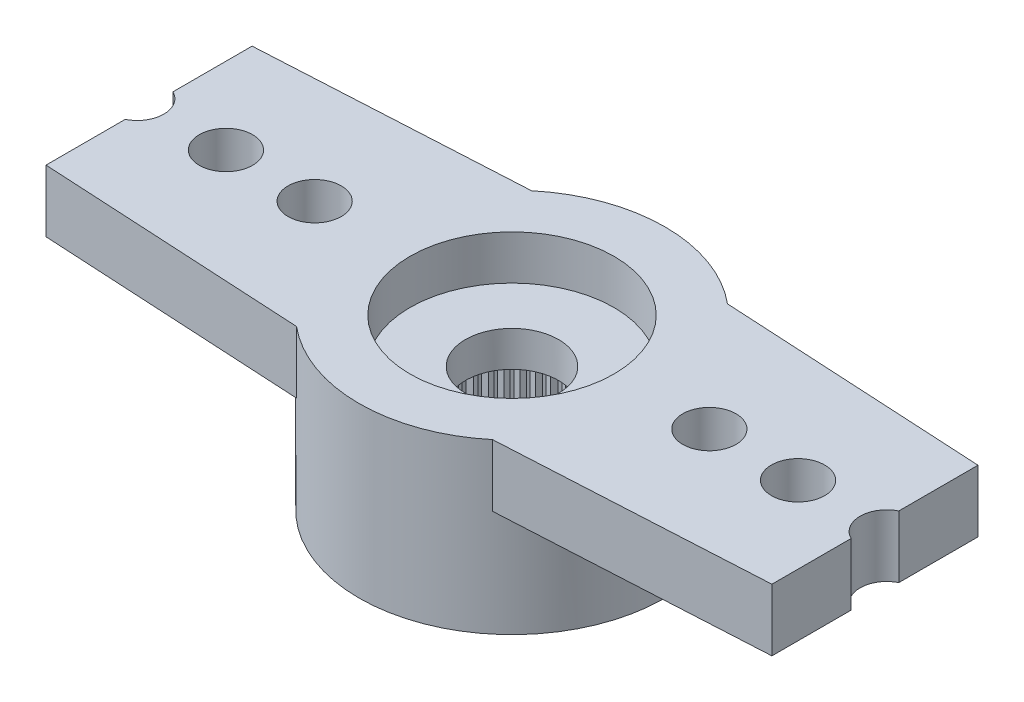
SolidWorks part; units mm, degrees
material "PVC Rígido"
ref_plane "Plano frontal" through (0, 0, 0) normal (0, 0, 1) x (1, 0, 0)
ref_plane "Plano superior" through (0, 0, 0) normal (0, 1, 0) x (1, 0, 0)
ref_plane "Plano direito" through (0, 0, 0) normal (1, 0, 0) x (0, 0, -1)
sketch "Esboço1" plane through (0, 0, 0) normal (0, 1, 0) x (1, 0, 0)
  line L0 (0, 0) -> (-14.05, 0) construction
  line L1 (-14.1591, 1.997) -> (-2.2091, 2.65)
  line L2 (-2.2091, -2.65) -> (-14.1591, -1.997)
  arc A0 (-2.2091, -2.65) -> (-2.2091, 2.65) centre (0, 0) ccw
  arc A1 (-14.1591, 1.997) -> (-14.1591, -1.997) centre (-14.05, 0) ccw
  dimension "D1" = 6.9
  dimension "D2" = 4
  dimension "D3" = 19.5
  dimension "D4" = 5.3
extrude "Ressalto-extrusão1" add sketch "Esboço1" against normal blind 1.4
sketch "Esboço2" plane through (0, -1.4, 0) normal (0, -1, 0) x (1, 0, 0)
  arc A0 (-2.2091, -2.65) -> (-2.2091, 2.65) centre (0, 0) ccw construction
  circle A1 centre (0, 0) radius 3.45
extrude "Ressalto-extrusão2" add sketch "Esboço2" along normal offset from surface (2.4 mm away) 3.8 up to face at (-7.242, 0, 0)
hole_wizard "Furo4" positions "Esboço9" profile "Esboço10" legacy end condition through all
sketch "Esboço9" plane through (0, 0, 0) normal (0, 1, 0) x (1, 0, 0)
  line L1 (-14.45, 0) -> (0, 0) construction
  arc A2 (-14.1591, 1.997) -> (-14.1591, -1.997) centre (-14.05, 0) ccw construction
  point P0 (-14.45, 0)
  point P19 (-16.05, 0)
  dimension "D1" = 1.6
sketch "Esboço10" plane through (-14.45, 0, 0) normal (1, 0, 0) x (0, 0, 1)
  line L0 (0, 0) -> (0, 3.8)
  line L1 (0, 3.8) -> (0.6, 3.8)
  line L2 (0.6, 3.8) -> (0.6, 0)
  line L3 (0.6, 0) -> (0, 0)
  line L4 (0, 110) -> (0, -10) construction
  dimension "Diameter" = 1.2
  dimension "Depth" = 3.8
pattern_linear "Padrão linear1" count 6 spacing 2 along (1, 0, 0) of "Furo4"
pattern_circular "PadrãoCircular2" count 2 over 360 about axis through (0, 0, 0) along (0, 1, 0) of "Ressalto-extrusão1", "Furo4", "Padrão linear1"
hole_wizard "Furo1" positions "Esboço3" profile "Esboço4" legacy
sketch "Esboço3" plane through (0, -3.8, 0) normal (0, -1, 0) x (-1, 0, 0)
  point P0 (0, 0)
sketch "Esboço4" plane through (0, -3.8, 0) normal (1, 0, 0) x (0, 0, -1)
  line L0 (0, 0) -> (0, 2)
  line L1 (0, 2) -> (2.475, 2)
  line L2 (2.475, 2) -> (2.475, 0)
  line L3 (2.475, 0) -> (0, 0)
  line L4 (0, 110) -> (0, -10) construction
  dimension "Diameter" = 4.95
  dimension "Depth" = 2
hole_wizard "Furo2" positions "Esboço5" profile "Esboço6" legacy
sketch "Esboço5" plane through (0, 0, 0) normal (0, 1, 0) x (1, 0, 0)
  point P0 (0, 0)
sketch "Esboço6" plane through (0, 0, 0) normal (1, 0, 0) x (0, 0, 1)
  line L0 (0, 0) -> (0, 1)
  line L1 (0, 1) -> (2.3, 1)
  line L2 (2.3, 1) -> (2.3, 0)
  line L3 (2.3, 0) -> (0, 0)
  line L4 (0, 110) -> (0, -10) construction
  dimension "Diameter" = 4.6
  dimension "Depth" = 1
hole_wizard "Furo3" positions "Esboço7" profile "Esboço8" legacy end condition through all
sketch "Esboço7" plane through (0, 0, 0) normal (0, 1, 0) x (1, 0, 0)
  point P0 (0, 0)
sketch "Esboço8" plane through (0, 0, 0) normal (1, 0, 0) x (0, 0, 1)
  line L0 (0, 0) -> (0, 3.8)
  line L1 (0, 3.8) -> (1.05, 3.8)
  line L2 (1.05, 3.8) -> (1.05, 0)
  line L3 (1.05, 0) -> (0, 0)
  line L4 (0, 110) -> (0, -10) construction
  dimension "Diameter" = 2.1
  dimension "Depth" = 3.8
sketch "Esboço11" plane through (0, -3.8, 0) normal (0, -1, 0) x (1, 0, 0)
  line L0 (-0.0981, 2.4731) -> (0, 2.375)
  line L1 (0, 2.375) -> (0.0981, 2.4731)
  line L2 (0, 0) -> (0, 2.475) construction
  circle A0 centre (0, 0) radius 2.375 construction
  circle A1 centre (0, 0) radius 2.475
  arc A2 (0.0981, 2.4731) -> (-0.0981, 2.4731) centre (0, 0) ccw
  dimension "D3" = 4.75
  dimension "D2" = 0.1
  dimension "D1" = 0
extrude "Ressalto-extrusão3" add sketch "Esboço11" against normal up to surface (2 mm away) up to face at (0, -1.8, 1.05)
pattern_circular "PadrãoCircular1" count 60 over 360 about axis through (0, 0, 0) along (0, 1, 0) of "Ressalto-extrusão3"
sketch "Szkic1" plane through (0, 0, 0) normal (0, 1, 0) x (1, 0, 0)
  line L0 (-8.1841, 2.3235) -> (-8.1841, -2.3235)
  line L1 (-2.2091, 2.65) -> (-14.1591, 1.997) construction
  line L2 (-14.1591, -1.997) -> (-2.2091, -2.65) construction
  line L3 (0, 0) -> (0, 3.45) construction
  line L4 (8.1841, 2.3235) -> (8.1841, -2.3235)
  line L5 (-8.1841, 2.3235) -> (-14.1591, 1.997)
  line L6 (-8.1841, -2.3235) -> (-14.1591, -1.997)
  line L7 (8.1841, -2.3235) -> (14.1591, -1.997)
  line L8 (8.1841, 2.3235) -> (14.1591, 1.997)
  arc A0 (-14.1591, 1.997) -> (-14.1591, -1.997) centre (-14.05, 0) ccw
  arc A1 (2.2091, 2.65) -> (-2.2091, 2.65) centre (0, 0) ccw construction
  arc A2 (14.1591, 1.997) -> (14.1591, -1.997) centre (14.05, 0) cw
  circle A3 centre (-6.45, 0) radius 0.6
  circle A4 centre (-4.45, 0) radius 0.6
  circle M6 centre (8.45, 0) radius 0.6
  circle M7 centre (10.45, 0) radius 0.6
  circle M8 centre (12.45, 0) radius 0.6
  circle M9 centre (14.45, 0) radius 0.6
  line M10 (-14.1591, -1.997) -> (-2.2091, -2.65)
  line M12 (2.2091, -2.65) -> (14.1591, -1.997)
  arc M13 (14.1591, -1.997) -> (14.1591, 1.997) centre (14.05, 0) ccw
  line M14 (14.1591, 1.997) -> (2.2091, 2.65)
  line M16 (-2.2091, 2.65) -> (-14.1591, 1.997)
  arc M17 (-14.1591, 1.997) -> (-14.1591, -1.997) centre (-14.05, 0) ccw
  circle M18 centre (-12.45, 0) radius 0.6
  circle M19 centre (-14.45, 0) radius 0.6
  circle M20 centre (-10.45, 0) radius 0.6
  circle M21 centre (-8.45, 0) radius 0.6
  dimension "D3" = 1.2
  dimension "D1" = 4.647
  dimension "D2" = 2
  dimension "D4" = 4.45
  dimension "D5" = 8.1841
extrude "Wytnij-wyciągnięcie1" cut sketch "Szkic1" against normal through all contours L0 M16 M17 M10 M21 M19 M20 M18 | L4 M14 M6 M12 M13 M8 M9 M7
